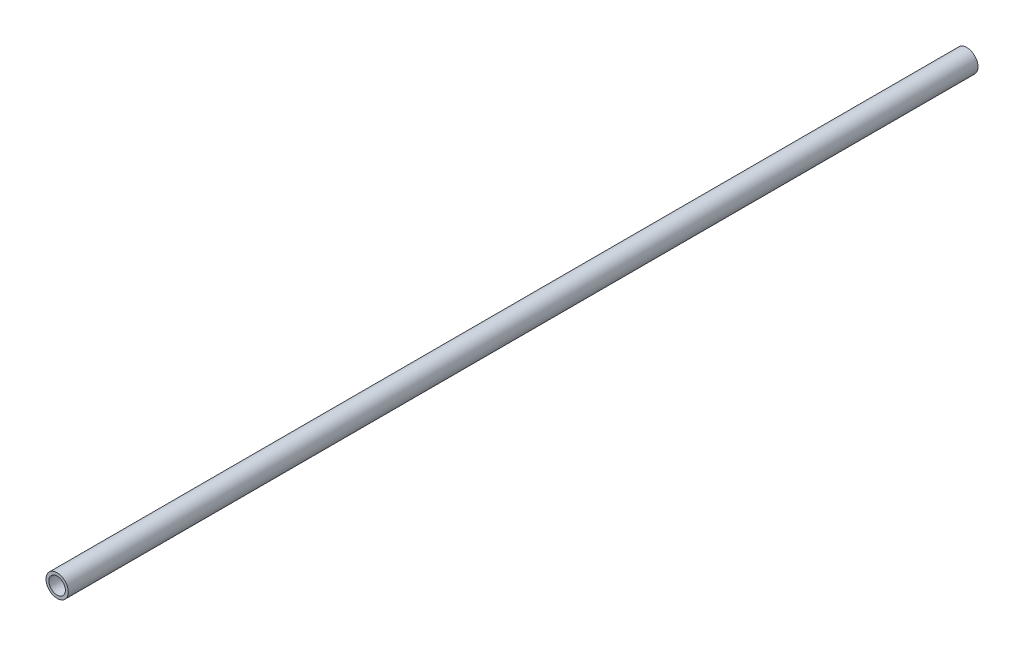
SolidWorks part; units mm, degrees
ref_plane "Front Plane" through (0, 0, 0) normal (0, 0, 1) x (1, 0, 0)
ref_plane "Top Plane" through (0, 0, 0) normal (0, 1, 0) x (1, 0, 0)
ref_plane "Right Plane" through (0, 0, 0) normal (1, 0, 0) x (0, 0, -1)
sketch "Sketch1" plane through (0, 0, 0) normal (0, 0, 1) x (1, 0, 0)
  circle A0 centre (0, 0) radius 10.668
  dimension "Pipe OD" = 21.336
extrude "Extrude-Thin1" add sketch "Sketch1" along normal mid plane 870 thin thin type one direction reverse wall 2.7686
